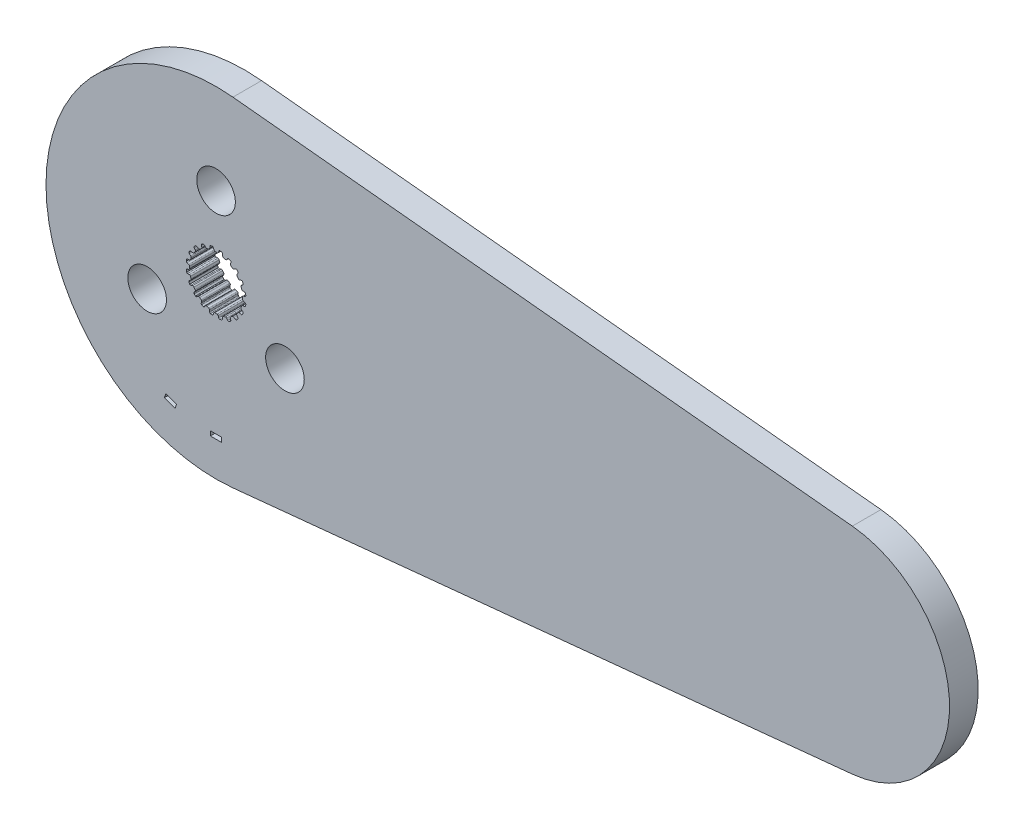
SolidWorks part; units mm, degrees
ref_plane "Front Plane" through (0, 0, 0) normal (0, 0, 1) x (1, 0, 0)
ref_plane "Top Plane" through (0, 0, 0) normal (0, 1, 0) x (1, 0, 0)
ref_plane "Right Plane" through (0, 0, 0) normal (1, 0, 0) x (0, 0, -1)
sketch "Sketch1" plane through (0, 0, 0) normal (0, 0, 1) x (1, 0, 0)
  line L0 (-0.1069, 2.9699) -> (0.1069, 2.9699)
  line L1 (0.3159, 3.2375) -> (0.2537, 3.0575)
  line L2 (-0.2964, 3.2367) -> (-0.2318, 3.0575)
  line L3 (-0.2964, 3.2367) -> (0.3159, 3.2375) construction
  line L4 (0, 3.3252) -> (0, 0) construction
  line L5 (-0.2318, 3.0575) -> (0.2537, 3.0575) construction
  line L6 (-0.4281, 3.3241) -> (0.4281, 3.3263) construction
  line L7 (0.7183, 3.1698) -> (0.7244, 2.9795)
  line L8 (0.816, 2.8576) -> (1.0195, 2.7915)
  line L9 (1.3009, 2.9815) -> (1.1862, 2.8295)
  line L10 (1.6627, 2.7927) -> (1.6097, 2.6099)
  line L11 (1.6591, 2.4655) -> (1.8322, 2.3398)
  line L12 (2.1585, 2.4335) -> (2.0025, 2.3245)
  line L13 (2.4443, 2.1423) -> (2.3374, 1.9847)
  line L14 (2.3398, 1.8322) -> (2.4655, 1.6591)
  line L15 (2.8049, 1.6474) -> (2.6228, 1.5919)
  line L16 (2.9866, 1.2821) -> (2.8363, 1.1653)
  line L17 (2.7915, 1.0195) -> (2.8576, 0.816)
  line L18 (3.1767, 0.7) -> (2.9863, 0.7035)
  line L19 (3.2367, 0.2964) -> (3.0575, 0.2318)
  line L20 (2.9699, 0.1069) -> (2.9699, -0.1069)
  line L21 (3.2375, -0.3159) -> (3.0575, -0.2537)
  line L22 (3.1698, -0.7183) -> (2.9795, -0.7244)
  line L23 (2.8576, -0.816) -> (2.7915, -1.0195)
  line L24 (2.9815, -1.3009) -> (2.8295, -1.1862)
  line L25 (2.7927, -1.6627) -> (2.6099, -1.6097)
  line L26 (2.4655, -1.6591) -> (2.3398, -1.8322)
  line L27 (2.4335, -2.1585) -> (2.3245, -2.0025)
  line L28 (2.1423, -2.4443) -> (1.9847, -2.3374)
  line L29 (1.8322, -2.3398) -> (1.6591, -2.4655)
  line L30 (1.6474, -2.8049) -> (1.5919, -2.6228)
  line L31 (1.2821, -2.9866) -> (1.1653, -2.8363)
  line L32 (1.0195, -2.7915) -> (0.816, -2.8576)
  line L33 (0.7, -3.1767) -> (0.7035, -2.9863)
  line L34 (0.2964, -3.2367) -> (0.2318, -3.0575)
  line L35 (0.1069, -2.9699) -> (-0.1069, -2.9699)
  line L36 (-0.3159, -3.2375) -> (-0.2537, -3.0575)
  line L37 (-0.7183, -3.1698) -> (-0.7244, -2.9795)
  line L38 (-0.816, -2.8576) -> (-1.0195, -2.7915)
  line L39 (-1.3009, -2.9815) -> (-1.1862, -2.8295)
  line L40 (-1.6627, -2.7927) -> (-1.6097, -2.6099)
  line L41 (-1.6591, -2.4655) -> (-1.8322, -2.3398)
  line L42 (-2.1585, -2.4335) -> (-2.0025, -2.3245)
  line L43 (-2.4443, -2.1423) -> (-2.3374, -1.9847)
  line L44 (-2.3398, -1.8322) -> (-2.4655, -1.6591)
  line L45 (-2.8049, -1.6474) -> (-2.6228, -1.5919)
  line L46 (-2.9866, -1.2821) -> (-2.8363, -1.1653)
  line L47 (-2.7915, -1.0195) -> (-2.8576, -0.816)
  line L48 (-3.1767, -0.7) -> (-2.9863, -0.7035)
  line L49 (-3.2367, -0.2964) -> (-3.0575, -0.2318)
  line L50 (-2.9699, -0.1069) -> (-2.9699, 0.1069)
  line L51 (-3.2375, 0.3159) -> (-3.0575, 0.2537)
  line L52 (-3.1698, 0.7183) -> (-2.9795, 0.7244)
  line L53 (-2.8576, 0.816) -> (-2.7915, 1.0195)
  line L54 (-2.9815, 1.3009) -> (-2.8295, 1.1862)
  line L55 (-2.7927, 1.6627) -> (-2.6099, 1.6097)
  line L56 (-2.4655, 1.6591) -> (-2.3398, 1.8322)
  line L57 (-2.4335, 2.1585) -> (-2.3245, 2.0025)
  line L58 (-2.1423, 2.4443) -> (-1.9847, 2.3374)
  line L59 (-1.8322, 2.3398) -> (-1.6591, 2.4655)
  line L60 (-1.6474, 2.8049) -> (-1.5919, 2.6228)
  line L61 (-1.2821, 2.9866) -> (-1.1653, 2.8363)
  line L62 (-1.0195, 2.7915) -> (-0.816, 2.8576)
  line L63 (-0.7, 3.1767) -> (-0.7035, 2.9863)
  line L64 (0.4281, 3.3263) -> (0.62, 3.2938)
  line L65 (1.4351, 3.0312) -> (1.6075, 2.9409)
  line L66 (2.3015, 2.4394) -> (2.4376, 2.3003)
  line L67 (2.9427, 1.6088) -> (3.0291, 1.4344)
  line L68 (3.2958, 0.6207) -> (3.3241, 0.4281)
  line L69 (3.3263, -0.4281) -> (3.2938, -0.62)
  line L70 (3.0312, -1.4351) -> (2.9409, -1.6075)
  line L71 (2.4394, -2.3015) -> (2.3003, -2.4376)
  line L72 (1.6088, -2.9427) -> (1.4344, -3.0291)
  line L73 (0.6207, -3.2958) -> (0.4281, -3.3241)
  line L74 (-0.4281, -3.3263) -> (-0.62, -3.2938)
  line L75 (-1.4351, -3.0312) -> (-1.6075, -2.9409)
  line L76 (-2.3015, -2.4394) -> (-2.4376, -2.3003)
  line L77 (-2.9427, -1.6088) -> (-3.0291, -1.4344)
  line L78 (-3.2958, -0.6207) -> (-3.3241, -0.4281)
  line L79 (-3.3263, 0.4281) -> (-3.2938, 0.62)
  line L80 (-3.0312, 1.4351) -> (-2.9409, 1.6075)
  line L81 (-2.4394, 2.3015) -> (-2.3003, 2.4376)
  line L82 (-1.6088, 2.9427) -> (-1.4344, 3.0291)
  line L83 (-0.6207, 3.2958) -> (-0.4281, 3.3241)
  line L84 (1.8866, 18.9078) -> (71.1016, 12.0015)
  line L85 (1.8866, -18.9078) -> (71.1016, -12.0015)
  line L86 (1.8866, 18.9078) -> (1.8866, -18.9078) construction
  line L87 (71.1016, 12.0015) -> (71.1016, -12.0015) construction
  arc A0 (0.2537, 3.0575) -> (0.1069, 2.9699) centre (0.1283, 3.1009) cw
  arc A1 (-0.2318, 3.0575) -> (-0.1069, 2.9699) centre (-0.1069, 3.1026) ccw
  arc A2 (0.62, 3.2938) -> (0.7183, 3.1698) centre (0.5856, 3.1656) cw
  arc A3 (0.7244, 2.9795) -> (0.816, 2.8576) centre (0.857, 2.9838) ccw
  arc A4 (-0.4281, 3.3241) -> (-0.2964, 3.2367) centre (-0.4213, 3.1916) cw
  arc A5 (0.4281, 3.3263) -> (0.3159, 3.2375) centre (0.4413, 3.1942) ccw
  arc A6 (1.1862, 2.8295) -> (1.0195, 2.7915) centre (1.0802, 2.9095) cw
  arc A7 (1.4351, 3.0312) -> (1.3009, 2.9815) centre (1.4068, 2.9015) ccw
  arc A8 (1.6075, 2.9409) -> (1.6627, 2.7927) centre (1.5352, 2.8297) cw
  arc A9 (1.6097, 2.6099) -> (1.6591, 2.4655) centre (1.7371, 2.5729) ccw
  arc A10 (2.0025, 2.3245) -> (1.8322, 2.3398) centre (1.9264, 2.4332) cw
  arc A11 (2.3015, 2.4394) -> (2.1585, 2.4335) centre (2.2346, 2.3248) ccw
  arc A12 (2.4376, 2.3003) -> (2.4443, 2.1423) centre (2.3345, 2.2168) cw
  arc A13 (2.3374, 1.9847) -> (2.3398, 1.8322) centre (2.4472, 1.9102) ccw
  arc A14 (2.6228, 1.5919) -> (2.4655, 1.6591) centre (2.5841, 1.7189) cw
  arc A15 (2.9427, 1.6088) -> (2.8049, 1.6474) centre (2.8436, 1.5205) ccw
  arc A16 (3.0291, 1.4344) -> (2.9866, 1.2821) centre (2.9052, 1.3869) cw
  arc A17 (2.8363, 1.1653) -> (2.7915, 1.0195) centre (2.9177, 1.0605) ccw
  arc A18 (2.9863, 0.7035) -> (2.8576, 0.816) centre (2.9887, 0.8362) cw
  arc A19 (3.2958, 0.6207) -> (3.1767, 0.7) centre (3.1743, 0.5673) ccw
  arc A20 (3.3241, 0.4281) -> (3.2367, 0.2964) centre (3.1916, 0.4213) cw
  arc A21 (3.0575, 0.2318) -> (2.9699, 0.1069) centre (3.1026, 0.1069) ccw
  arc A22 (3.0575, -0.2537) -> (2.9699, -0.1069) centre (3.1009, -0.1283) cw
  arc A23 (3.3263, -0.4281) -> (3.2375, -0.3159) centre (3.1942, -0.4413) ccw
  arc A24 (3.2938, -0.62) -> (3.1698, -0.7183) centre (3.1656, -0.5856) cw
  arc A25 (2.9795, -0.7244) -> (2.8576, -0.816) centre (2.9838, -0.857) ccw
  arc A26 (2.8295, -1.1862) -> (2.7915, -1.0195) centre (2.9095, -1.0802) cw
  arc A27 (3.0312, -1.4351) -> (2.9815, -1.3009) centre (2.9015, -1.4068) ccw
  arc A28 (2.9409, -1.6075) -> (2.7927, -1.6627) centre (2.8297, -1.5352) cw
  arc A29 (2.6099, -1.6097) -> (2.4655, -1.6591) centre (2.5729, -1.7371) ccw
  arc A30 (2.3245, -2.0025) -> (2.3398, -1.8322) centre (2.4332, -1.9264) cw
  arc A31 (2.4394, -2.3015) -> (2.4335, -2.1585) centre (2.3248, -2.2346) ccw
  arc A32 (2.3003, -2.4376) -> (2.1423, -2.4443) centre (2.2168, -2.3345) cw
  arc A33 (1.9847, -2.3374) -> (1.8322, -2.3398) centre (1.9102, -2.4472) ccw
  arc A34 (1.5919, -2.6228) -> (1.6591, -2.4655) centre (1.7189, -2.5841) cw
  arc A35 (1.6088, -2.9427) -> (1.6474, -2.8049) centre (1.5205, -2.8436) ccw
  arc A36 (1.4344, -3.0291) -> (1.2821, -2.9866) centre (1.3869, -2.9052) cw
  arc A37 (1.1653, -2.8363) -> (1.0195, -2.7915) centre (1.0605, -2.9177) ccw
  arc A38 (0.7035, -2.9863) -> (0.816, -2.8576) centre (0.8362, -2.9887) cw
  arc A39 (0.6207, -3.2958) -> (0.7, -3.1767) centre (0.5673, -3.1743) ccw
  arc A40 (0.4281, -3.3241) -> (0.2964, -3.2367) centre (0.4213, -3.1916) cw
  arc A41 (0.2318, -3.0575) -> (0.1069, -2.9699) centre (0.1069, -3.1026) ccw
  arc A42 (-0.2537, -3.0575) -> (-0.1069, -2.9699) centre (-0.1283, -3.1009) cw
  arc A43 (-0.4281, -3.3263) -> (-0.3159, -3.2375) centre (-0.4413, -3.1942) ccw
  arc A44 (-0.62, -3.2938) -> (-0.7183, -3.1698) centre (-0.5856, -3.1656) cw
  arc A45 (-0.7244, -2.9795) -> (-0.816, -2.8576) centre (-0.857, -2.9838) ccw
  arc A46 (-1.1862, -2.8295) -> (-1.0195, -2.7915) centre (-1.0802, -2.9095) cw
  arc A47 (-1.4351, -3.0312) -> (-1.3009, -2.9815) centre (-1.4068, -2.9015) ccw
  arc A48 (-1.6075, -2.9409) -> (-1.6627, -2.7927) centre (-1.5352, -2.8297) cw
  arc A49 (-1.6097, -2.6099) -> (-1.6591, -2.4655) centre (-1.7371, -2.5729) ccw
  arc A50 (-2.0025, -2.3245) -> (-1.8322, -2.3398) centre (-1.9264, -2.4332) cw
  arc A51 (-2.3015, -2.4394) -> (-2.1585, -2.4335) centre (-2.2346, -2.3248) ccw
  arc A52 (-2.4376, -2.3003) -> (-2.4443, -2.1423) centre (-2.3345, -2.2168) cw
  arc A53 (-2.3374, -1.9847) -> (-2.3398, -1.8322) centre (-2.4472, -1.9102) ccw
  arc A54 (-2.6228, -1.5919) -> (-2.4655, -1.6591) centre (-2.5841, -1.7189) cw
  arc A55 (-2.9427, -1.6088) -> (-2.8049, -1.6474) centre (-2.8436, -1.5205) ccw
  arc A56 (-3.0291, -1.4344) -> (-2.9866, -1.2821) centre (-2.9052, -1.3869) cw
  arc A57 (-2.8363, -1.1653) -> (-2.7915, -1.0195) centre (-2.9177, -1.0605) ccw
  arc A58 (-2.9863, -0.7035) -> (-2.8576, -0.816) centre (-2.9887, -0.8362) cw
  arc A59 (-3.2958, -0.6207) -> (-3.1767, -0.7) centre (-3.1743, -0.5673) ccw
  arc A60 (-3.3241, -0.4281) -> (-3.2367, -0.2964) centre (-3.1916, -0.4213) cw
  arc A61 (-3.0575, -0.2318) -> (-2.9699, -0.1069) centre (-3.1026, -0.1069) ccw
  arc A62 (-3.0575, 0.2537) -> (-2.9699, 0.1069) centre (-3.1009, 0.1283) cw
  arc A63 (-3.3263, 0.4281) -> (-3.2375, 0.3159) centre (-3.1942, 0.4413) ccw
  arc A64 (-3.2938, 0.62) -> (-3.1698, 0.7183) centre (-3.1656, 0.5856) cw
  arc A65 (-2.9795, 0.7244) -> (-2.8576, 0.816) centre (-2.9838, 0.857) ccw
  arc A66 (-2.8295, 1.1862) -> (-2.7915, 1.0195) centre (-2.9095, 1.0802) cw
  arc A67 (-3.0312, 1.4351) -> (-2.9815, 1.3009) centre (-2.9015, 1.4068) ccw
  arc A68 (-2.9409, 1.6075) -> (-2.7927, 1.6627) centre (-2.8297, 1.5352) cw
  arc A69 (-2.6099, 1.6097) -> (-2.4655, 1.6591) centre (-2.5729, 1.7371) ccw
  arc A70 (-2.3245, 2.0025) -> (-2.3398, 1.8322) centre (-2.4332, 1.9264) cw
  arc A71 (-2.4394, 2.3015) -> (-2.4335, 2.1585) centre (-2.3248, 2.2346) ccw
  arc A72 (-2.3003, 2.4376) -> (-2.1423, 2.4443) centre (-2.2168, 2.3345) cw
  arc A73 (-1.9847, 2.3374) -> (-1.8322, 2.3398) centre (-1.9102, 2.4472) ccw
  arc A74 (-1.5919, 2.6228) -> (-1.6591, 2.4655) centre (-1.7189, 2.5841) cw
  arc A75 (-1.6088, 2.9427) -> (-1.6474, 2.8049) centre (-1.5205, 2.8436) ccw
  arc A76 (-1.4344, 3.0291) -> (-1.2821, 2.9866) centre (-1.3869, 2.9052) cw
  arc A77 (-1.1653, 2.8363) -> (-1.0195, 2.7915) centre (-1.0605, 2.9177) ccw
  arc A78 (-0.7035, 2.9863) -> (-0.816, 2.8576) centre (-0.8362, 2.9887) cw
  arc A79 (-0.6207, 3.2958) -> (-0.7, 3.1767) centre (-0.5673, 3.1743) ccw
  circle A80 centre (0, 0) radius 12.7 construction
  arc A81 (1.8866, 18.9078) -> (1.8866, -18.9078) centre (0, 0) ccw
  arc A82 (71.1016, 12.0015) -> (71.1016, -12.0015) centre (69.9041, 0) cw
  point P14 (0, 2.9699)
  point P247 (0, 0)
  point P250 (0, 0)
  dimension "D4" = 0.1327
  dimension "D8" = 20
  dimension "D9" = 25.4
  dimension "D1" = 2.9699
  dimension "D2" = 0.2139
  dimension "D3" = 0.1904
  dimension "D5" = 0.0877
  dimension "D6" = 0.4855
  dimension "D7" = 0.8563
  dimension "D10" = 37.8155
  dimension "D11" = 24.003
  dimension "D12" = 69.215
extrude "Boss-Extrude1" add sketch "Sketch1" along normal blind 3.2004
sketch "Sketch2" plane through (0, 0, 3.2004) normal (0, 0, 1) x (1, 0, 0)
  line L0 (-5.1796, -14.2308) -> (0, 0) construction
  line L1 (-4.5829, -14.448) -> (-4.4091, -13.9706)
  line L2 (-4.4091, -13.9706) -> (-5.6025, -13.5362)
  line L3 (-5.6025, -13.5362) -> (-5.7763, -14.0136)
  line L4 (-5.7763, -14.0136) -> (-4.5829, -14.448)
  line L5 (0, 3.3252) -> (0, 0) construction
  line L6 (0, -15.1441) -> (0, 0) construction
  line L7 (0.635, -15.1441) -> (0.635, -14.6361)
  line L8 (0.635, -14.6361) -> (-0.635, -14.6361)
  line L9 (-0.635, -14.6361) -> (-0.635, -15.1441)
  line L10 (-0.635, -15.1441) -> (0.635, -15.1441)
  circle A1 centre (0, 0) radius 12.7 construction
  dimension "D1" = 1.27
  dimension "D2" = 0.508
  dimension "D3" = 20
  dimension "D4" = 15.1441
extrude "Cut-Extrude1" cut sketch "Sketch2" against normal up to surface (3.2004 mm away) up to face at (33.9879, 0, 0)
sketch "Sketch3" plane through (0, 0, 3.2004) normal (0, 0, 1) x (1, 0, 0)
  line L0 (0, 8.89) -> (0, 0) construction
  line L2 (0, 3.3252) -> (0, 0) construction
  circle A1 centre (0, 8.89) radius 2.159
  circle A4 centre (0, 0) radius 12.7 construction
  circle A5 centre (7.699, -4.445) radius 2.159
  circle A6 centre (-7.699, -4.445) radius 2.159
  point P13 (0, 0)
  dimension "D2" = 4.318
  dimension "D1" = 8.89
  dimension "D3" = 3
extrude "Cut-Extrude2" cut sketch "Sketch3" against normal up to surface (3.2004 mm away) up to face at (-5.0927, -13.9921, 0)
